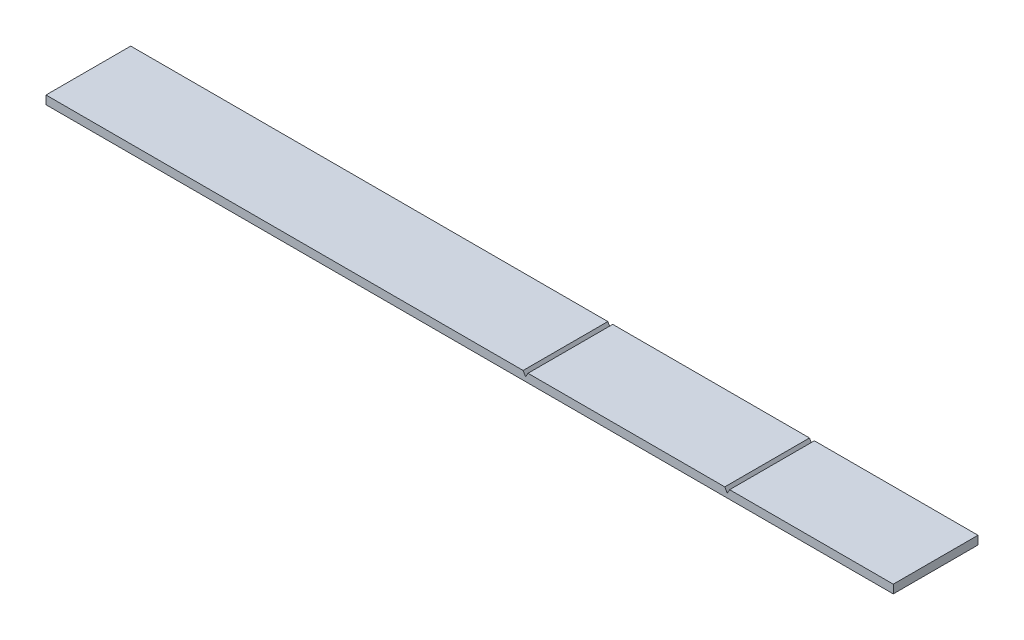
SolidWorks part; units mm, degrees
ref_plane "Front" through (0, 0, 0) normal (0, 0, 1) x (1, 0, 0)
ref_plane "Top" through (0, 0, 0) normal (0, 1, 0) x (1, 0, 0)
ref_plane "Right" through (0, 0, 0) normal (1, 0, 0) x (0, 0, -1)
sketch "Sketch1" plane through (0, 0, 0) normal (0, 0, 1) x (1, 0, 0)
  line L0 (566, 0) -> (566, -5) construction
  line L1 (0, 0) -> (563.1132, 0)
  line L2 (0, 0) -> (0, -10)
  line L3 (0, -10) -> (1000, -10)
  line L4 (1000, 0) -> (1000, -10)
  line L5 (804, 0) -> (804, -5) construction
  line L6 (563.1132, 0) -> (566, -5)
  line L7 (566, -5) -> (568.8868, 0)
  line L8 (801.1132, 0) -> (804, -5)
  line L9 (804, -5) -> (806.8868, 0)
  line L10 (568.8868, 0) -> (801.1132, 0)
  line L11 (806.8868, 0) -> (1000, 0)
  point P4 (566, 0)
  point P5 (804, 0)
  dimension "D1" = 10
  dimension "D2" = 1000
  dimension "D3" = 566
  dimension "D4" = 804
  dimension "D5" = 60
  dimension "D6" = 60
  dimension "D7" = 60
  dimension "D8" = 60
  dimension "D9" = 5
  dimension "D10" = 5
extrude "Boss-Extrude1" add sketch "Sketch1" along normal blind 100
